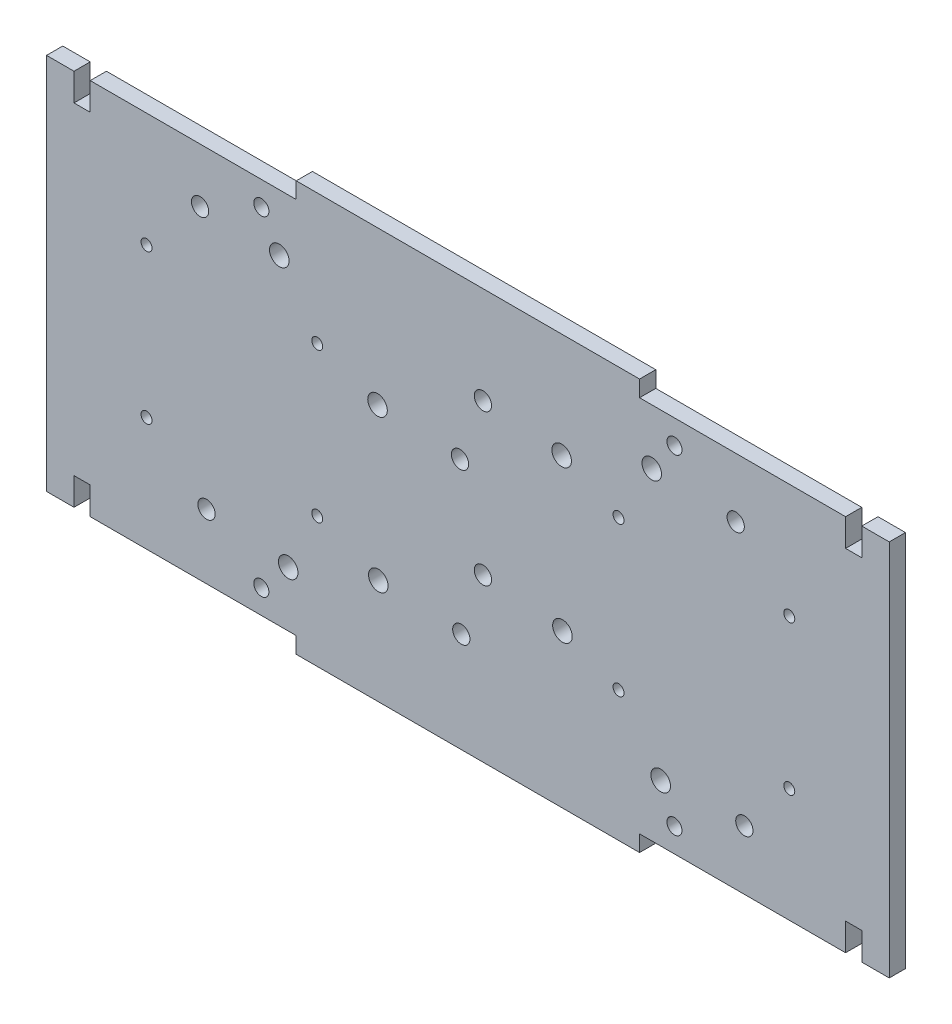
SolidWorks part; units mm, degrees
ref_plane "Front Plane" through (0, 0, 0) normal (0, 0, 1) x (1, 0, 0)
ref_plane "Top Plane" through (0, 0, 0) normal (0, 1, 0) x (1, 0, 0)
ref_plane "Right Plane" through (0, 0, 0) normal (1, 0, 0) x (0, 0, -1)
sketch "Sketch3" plane through (0, 0, 0) normal (0, 0, 1) x (1, 0, 0)
  line L0 (38.1, 0) -> (38.1, -2.9972)
  line L1 (38.1, -2.9972) -> (101.6, -2.9972) construction
  line L4 (38.1, 72.8472) -> (101.6, 72.8472) construction
  line L6 (101.6, -2.9972) -> (101.6, 0)
  line L7 (38.1, -2.9972) -> (101.6, -2.9972)
  line L8 (38.1, 69.85) -> (38.1, 72.8472)
  line L9 (101.6, 69.85) -> (101.6, 72.8472)
  line L10 (38.1, 72.8472) -> (101.6, 72.8472)
  line L12 (38.1, 69.85) -> (0, 69.85)
  line L13 (0, 69.85) -> (0, 64.77)
  line L14 (0, 64.77) -> (-2.9972, 64.77)
  line L15 (-2.9972, 64.77) -> (-2.9972, 69.85)
  line L16 (-2.9972, 69.85) -> (-8.0772, 69.85)
  line L17 (-8.0772, 69.85) -> (-8.0772, 0)
  line L18 (-8.0772, 0) -> (-2.9972, 0)
  line L19 (-2.9972, 0) -> (-2.9972, 5.08)
  line L20 (-2.9972, 5.08) -> (0, 5.08)
  line L21 (0, 5.08) -> (0, 0)
  line L22 (0, 0) -> (38.1, 0)
  line L23 (69.85, 72.8472) -> (69.85, -2.9972) construction
  line L24 (139.7, 0) -> (101.6, 0)
  line L25 (139.7, 5.08) -> (139.7, 0)
  line L26 (142.6972, 5.08) -> (139.7, 5.08)
  line L27 (142.6972, 0) -> (142.6972, 5.08)
  line L28 (147.7772, 0) -> (142.6972, 0)
  line L29 (147.7772, 69.85) -> (147.7772, 0)
  line L30 (142.6972, 69.85) -> (147.7772, 69.85)
  line L31 (142.6972, 64.77) -> (142.6972, 69.85)
  line L32 (139.7, 64.77) -> (142.6972, 64.77)
  line L33 (139.7, 69.85) -> (139.7, 64.77)
  line L34 (101.6, 69.85) -> (139.7, 69.85)
  dimension "D1" = 5.08
  dimension "D2" = 2.9972
  dimension "D3" = 2.9972
extrude "Boss-Extrude1" add sketch "Sketch3" along normal blind 2.9972
sketch "Sketch4" plane through (0, 0, 2.9972) normal (0, 0, 1) x (1, 0, 0)
  line L0 (-8.0772, -3.175) -> (-2.9972, -3.175)
  line L1 (-2.9972, -3.175) -> (-2.9972, 0)
  line L2 (-13.1572, 73.025) -> (-8.0772, 73.025)
  line L3 (-13.1572, 62.865) -> (-8.0772, 62.865)
  line L4 (-8.0772, 69.85) -> (-8.0772, 0) construction
  line L5 (-8.0772, 73.025) -> (-8.0772, 62.865)
  line L6 (-8.0772, 34.925) -> (147.7772, 34.925) construction
  line L7 (147.7772, 0) -> (147.7772, 69.85) construction
  line L8 (69.85, 72.8472) -> (69.85, -2.9972) construction
  line L9 (101.6, 72.8472) -> (38.1, 72.8472) construction
  line L10 (38.1, -2.9972) -> (101.6, -2.9972) construction
  line L11 (-8.0772, -3.175) -> (-8.0772, 6.985)
  line L12 (-13.1572, 6.985) -> (-8.0772, 6.985)
  line L13 (-13.1572, -3.175) -> (-8.0772, -3.175)
  line L14 (152.8572, -3.175) -> (147.7772, -3.175)
  line L15 (152.8572, 6.985) -> (147.7772, 6.985)
  line L16 (147.7772, -3.175) -> (147.7772, 6.985)
  line L17 (147.7772, 73.025) -> (147.7772, 62.865)
  line L18 (152.8572, 62.865) -> (147.7772, 62.865)
  line L19 (152.8572, 73.025) -> (147.7772, 73.025)
  line L20 (-2.9972, 0) -> (-8.0772, 0)
  line L21 (-8.0772, 73.025) -> (-2.9972, 73.025)
  line L22 (-2.9972, 73.025) -> (-2.9972, 69.85)
  line L23 (-2.9972, 69.85) -> (-8.0772, 69.85)
  circle A0 centre (-13.1572, 67.945) radius 5.08
  circle A1 centre (-13.1572, 1.905) radius 5.08
  circle A2 centre (152.8572, 1.905) radius 5.08
  circle A3 centre (152.8572, 67.945) radius 5.08
  dimension "D1" = 10.16
  dimension "D2" = 5.08
  dimension "D3" = 66.04
extrude "Boss-Extrude2" [suppressed] add sketch "Sketch4" against normal up to vertex
sketch "Sketch5" [suppressed] plane through (0, 0, 2.9972) normal (0, 0, 1) x (1, 0, 0)
  line L3 (-13.1572, 67.945) -> (-13.1572, 73.025) construction
  circle A0 centre (-13.1572, 67.945) radius 2.54
  circle A1 centre (-13.1572, 1.905) radius 2.54
  arc A2 (-13.1572, 73.025) -> (-13.1572, 62.865) centre (-13.1572, 67.945) ccw construction
  arc A3 (-13.1572, 6.985) -> (-13.1572, -3.175) centre (-13.1572, 1.905) ccw construction
  circle A4 centre (140.1572, 67.945) radius 2.54
  circle A5 centre (140.1572, 1.905) radius 2.54
  arc A6 (140.1572, -3.175) -> (140.1572, 6.985) centre (140.1572, 1.905) ccw construction
  arc A7 (140.1572, 62.865) -> (140.1572, 73.025) centre (140.1572, 67.945) ccw construction
  dimension "D1" = 5.08
extrude "Cut-Extrude1" [suppressed] cut sketch "Sketch5" against normal through all
sketch "Sketch6" plane through (0, 0, 0) normal (0, 0, -1) x (-1, 0, 0)
  line L0 (-131.445, 2.413) -> (-8.255, 67.437) construction
  line L1 (-139.7, 69.85) -> (0, 69.85) construction
  line L2 (-139.7, 69.85) -> (-139.7, 0) construction
  line L3 (-139.7, 0) -> (0, 0) construction
  line L4 (0, 69.85) -> (0, 0) construction
  line L5 (-131.445, 67.437) -> (-8.255, 67.437)
  line L6 (-131.445, 67.437) -> (-131.445, 2.413)
  line L7 (-131.445, 2.413) -> (-8.255, 2.413)
  line L8 (-8.255, 67.437) -> (-8.255, 2.413)
  line L9 (-139.7, 69.85) -> (0, 0) construction
  circle A0 centre (-101.6318, 59.0613) radius 1.8097
  circle A1 centre (-104.5718, 11.1315) radius 1.8097
  circle A2 centre (-48.7617, 16.4655) radius 1.8097
  circle A3 centre (-51.3652, 44.4817) radius 1.8097
  point P10 (-69.85, 34.925)
  point P11 (-69.85, 34.925)
  dimension "D3" = 6.5659
  dimension "D4" = 28.0035
  dimension "D5" = 26.8732
  dimension "D6" = 6.9088
  dimension "D7" = 12.2428
  dimension "D8" = 38.6969
  dimension "D9" = 21.1455
  dimension "D10" = 78.2701
  dimension "D11" = 3.6195
  dimension "D1" = 123.19
  dimension "D2" = 65.024
extrude "Cut-Extrude2" [suppressed] cut sketch "Sketch6" against normal through all contours A0 | A3 | A2 | A1
sketch "Sketch7" plane through (0, 0, 0) normal (0, 0, -1) x (-1, 0, 0)
  line L0 (-63.5, 69.85) -> (-63.5, 0) construction
ref_plane "Plane2" through (63.5, 0, 0) normal (-1, 0, 0) x (0, 0, 1)
mirror "Mirror1" [suppressed] about plane through (63.5, 0, 0) normal (-1, 0, 0)
sketch "Sketch9" plane through (0, 0, 0) normal (0, 0, -1) x (-1, 0, 0)
  line L0 (-31.6484, 65.405) -> (-31.6484, 4.445) construction
  line L2 (-108.0516, 65.405) -> (-108.0516, 69.8215) construction
  line L3 (-108.0516, 65.405) -> (-108.0516, 4.445) construction
  line L5 (-69.85, 69.85) -> (-69.85, 0) construction
  line L6 (-108.0516, 69.8215) -> (-31.6484, 69.8785) construction
  line L7 (-101.6, 72.8472) -> (-38.1, 72.8472) construction
  line L8 (-31.6484, 69.8785) -> (-31.6484, 65.405) construction
  line L9 (-147.7772, 0) -> (8.0772, 0) construction
  line L10 (8.0772, 34.925) -> (-69.85, 34.925) construction
  line L11 (8.0772, 69.85) -> (8.0772, 0) construction
  line L12 (-69.85, 34.925) -> (-108.0516, 34.925) construction
  circle A0 centre (-31.6484, 4.445) radius 1.397
  circle A1 centre (-108.0516, 65.405) radius 1.397
  circle A2 centre (-108.0516, 4.445) radius 1.397
  circle A3 centre (-31.6484, 65.405) radius 1.397
  dimension "D2" = 2.794
  dimension "D3" = 6.0452
  dimension "D4" = 79.1972
extrude "Cut-Extrude3" cut sketch "Sketch9" against normal through all
sketch "Sketch10" plane through (0, 0, 0) normal (0, 0, -1) x (-1, 0, 0)
  line L0 (-131.445, 67.437) -> (-139.7, 67.437)
  line L1 (-139.7, 64.77) -> (-139.7, 69.85) construction
  line L2 (-8.255, 2.413) -> (0, 2.413) construction
  line L3 (0, 5.08) -> (0, 0) construction
  line L4 (-131.445, 69.85) -> (-131.445, 67.437) construction
  line L5 (-139.7, 69.85) -> (-101.6, 69.85) construction
  line L6 (-8.255, 2.413) -> (-8.255, 0) construction
  line L7 (0, 0) -> (-38.1, 0) construction
  line L8 (-69.85, 72.8472) -> (-69.85, -2.9972) construction
  line L9 (-101.6, 72.8472) -> (-38.1, 72.8472) construction
  line L10 (-38.1, -2.9972) -> (-101.6, -2.9972) construction
  line L11 (8.0772, 34.925) -> (-147.7772, 34.925) construction
  line L12 (8.0772, 69.85) -> (8.0772, 0) construction
  line L13 (-147.7772, 0) -> (-147.7772, 69.85) construction
  line B0 (-53.1368, 46.2915) -> (-53.1368, 67.437) construction
  line B1 (-131.445, 2.413) -> (-8.255, 2.413) construction
  line B2 (-131.445, 2.413) -> (-131.445, 67.437) construction
  line B3 (-131.445, 67.437) -> (-8.255, 67.437) construction
  line B4 (-8.255, 2.413) -> (-8.255, 67.437) construction
  line B5 (-51.3271, 44.4818) -> (-8.255, 44.4818) construction
  line B6 (-105.5053, 8.6995) -> (-105.5053, 2.413) construction
  line B7 (-107.315, 10.5093) -> (-131.445, 10.5092) construction
  line B8 (-103.8543, 61.4426) -> (-103.8543, 67.437) construction
  line B9 (-105.664, 59.6328) -> (-131.445, 59.6328) construction
  line B10 (-51.4731, 16.4401) -> (-8.255, 16.4401) construction
  line B11 (-53.2829, 14.6304) -> (-53.2829, 2.413) construction
  circle B12 centre (-103.8543, 59.6328) radius 1.8098
  circle B13 centre (-53.1368, 44.4818) radius 1.8097
  circle B14 centre (-53.2829, 16.4401) radius 1.8097
  circle B15 centre (-105.5053, 10.5093) radius 1.8097
  line B16 (-87.3358, 23.5585) -> (-87.3358, 2.413) construction
  line B17 (-9.0276, 67.437) -> (-132.2176, 67.437) construction
  line B18 (-9.0276, 67.437) -> (-9.0276, 2.413) construction
  line B19 (-9.0276, 2.413) -> (-132.2176, 2.413) construction
  line B20 (-132.2176, 67.437) -> (-132.2176, 2.413) construction
  line B21 (-89.1456, 25.3682) -> (-132.2176, 25.3682) construction
  line B22 (-34.9674, 61.1505) -> (-34.9674, 67.437) construction
  line B23 (-33.1576, 59.3407) -> (-9.0276, 59.3407) construction
  line B24 (-36.6184, 8.4074) -> (-36.6184, 2.413) construction
  line B25 (-34.8086, 10.2172) -> (-9.0276, 10.2172) construction
  line B26 (-88.9995, 53.4098) -> (-132.2176, 53.4098) construction
  line B27 (-87.1898, 55.2196) -> (-87.1898, 67.437) construction
  circle B28 centre (-36.6184, 10.2172) radius 1.8098
  circle B29 centre (-87.3358, 25.3682) radius 1.8097
  circle B30 centre (-87.1898, 53.4098) radius 1.8097
  circle B31 centre (-34.9674, 59.3407) radius 1.8097
sketch_block_instance "Prduino Holes-1"
sketch_block "Prduino Holes" parameters "D1"=3.6195, "D2"=123.19, "D3"=65.024, "D4"=78.3082, "D5"=21.1455, "D6"=12.2174, "D7"=24.13, "D8"=6.2865, "D9"=25.781, "D10"=5.9944, "D11"=76.3524
sketch_block_instance "Prduino Holes-4"
extrude "Cut-Extrude4" cut sketch "Sketch10" against normal through all contours B13 | B31 | B30 | B12 | B29 | B15 | B14 | B28
ref_plane "Plane3" through (0, 34.925, 0) normal (0, 1, 0) x (1, 0, 0)
sketch "Sketch11" plane through (0, 0, 0) normal (0, 0, -1) x (-1, 0, 0)
  line L0 (-119.38, 58.864) -> (-119.38, 10.986) construction
  line L1 (-119.38, 34.925) -> (-68.3906, 34.925) construction
  line L2 (-68.3906, 34.925) -> (-68.3906, 43.3869) construction
  line L3 (-69.85, 72.8472) -> (-69.85, 34.925) construction
  line L4 (-101.6, 72.8472) -> (-38.1, 72.8472) construction
  line L5 (-119.38, 34.925) -> (-147.7772, 34.925) construction
  line L6 (-147.7772, 0) -> (-147.7772, 69.85) construction
  line L7 (-139.7, 64.77) -> (-139.7, 69.85) construction
  line L8 (0, 69.85) -> (0, 64.77) construction
  circle B0 centre (-119.38, 58.864) radius 1.6
  circle B1 centre (-120.98, 10.986) radius 1.6
  circle B2 centre (-68.6295, 15.4879) radius 1.6
  circle B3 centre (-68.3906, 43.3869) radius 1.6
  circle B4 centre (-21.51, 11.9505) radius 1.6
  circle B5 centre (-20.32, 59.8405) radius 1.6
  circle B6 centre (-72.63, 54.8905) radius 1.6
  circle B7 centre (-72.63, 26.9905) radius 1.6
  dimension "D1" = 20.32
  dimension "D2" = 20.32
sketch_block_instance "Arduino Uno Mega Holes-1"
sketch_block "Arduino Uno Mega Holes"
sketch_block_instance "Arduino Uno Mega Holes-5"
extrude "Cut-Extrude5" cut sketch "Sketch11" against normal through all
sketch "Sketch12" plane through (0, 0, 2.9972) normal (0, 0, 1) x (1, 0, 0)
  line L0 (0, 64.77) -> (0, 5.08) construction
  line L1 (0, 34.925) -> (8.89, 34.925) construction
  line L2 (69.85, 72.8472) -> (69.85, -2.9972) construction
  line L3 (101.6, 72.8472) -> (38.1, 72.8472) construction
  line L4 (38.1, -2.9972) -> (101.6, -2.9972) construction
  line L6 (139.7, 64.77) -> (139.7, 5.08) construction
  circle B0 centre (10.414, 21.1074) radius 1.016
  circle B1 centre (10.414, 48.7426) radius 1.016
  circle B2 centre (41.9862, 21.1074) radius 1.016
  circle B3 centre (41.9862, 48.7426) radius 1.016
  circle B4 centre (129.286, 21.1074) radius 1.016
  circle B5 centre (129.286, 48.7426) radius 1.016
  circle B6 centre (97.7138, 21.1074) radius 1.016
  circle B7 centre (97.7138, 48.7426) radius 1.016
  dimension "D1" = 8.89
sketch_block_instance "Camera Mount-1"
sketch_block "Camera Mount" parameters "D1"=2.032, "D2"=33.6042, "D3"=29.6672
sketch_block_instance "Camera Mount-4"
extrude "Cut-Extrude6" cut sketch "Sketch12" against normal through all
